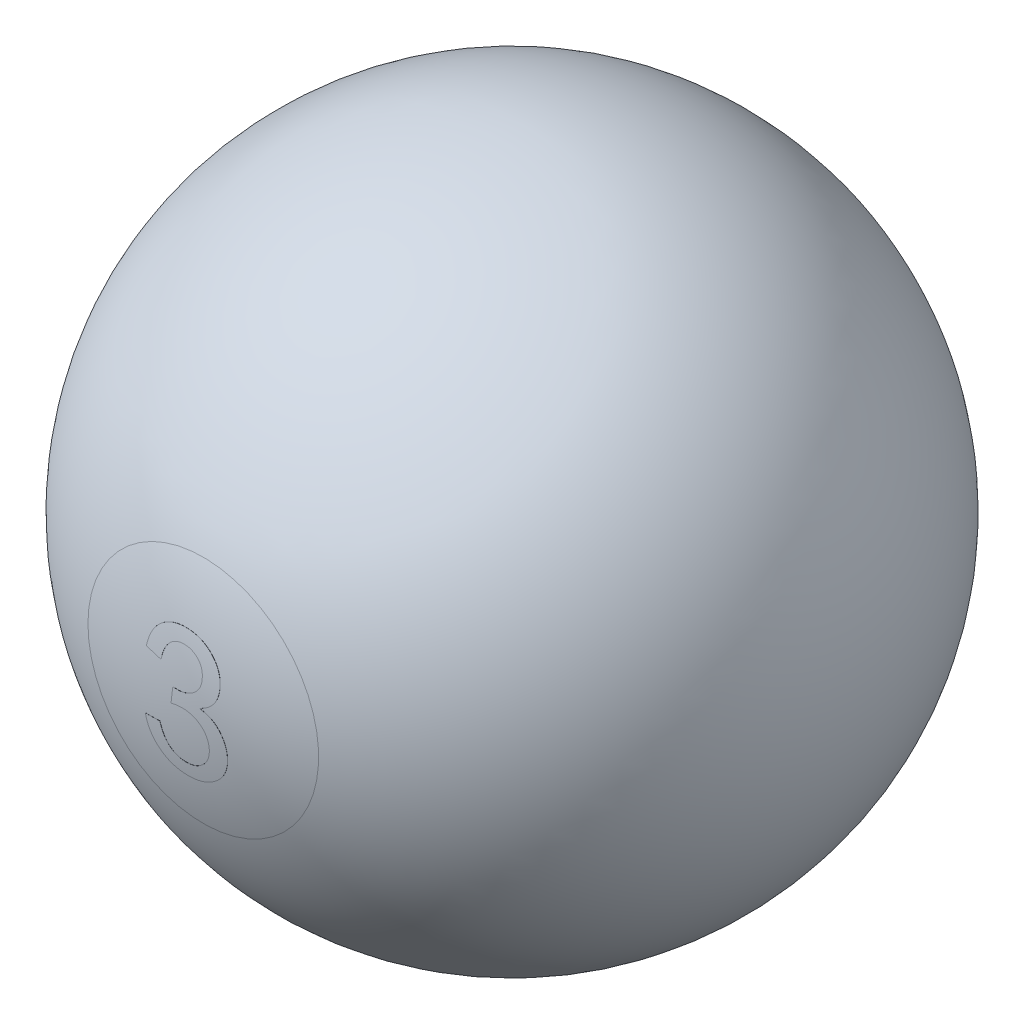
SolidWorks part; units mm, degrees
ref_plane "Vorne" through (0, 0, 0) normal (0, 0, 1) x (1, 0, 0)
ref_plane "Oben" through (0, 0, 0) normal (0, 1, 0) x (1, 0, 0)
ref_plane "Rechts" through (0, 0, 0) normal (1, 0, 0) x (0, 0, -1)
sketch "Skizze1" plane through (0, 0, 0) normal (0, 0, 1) x (1, 0, 0)
  line L0 (0, 0) -> (34.9607, 0) construction
  line L1 (28.575, 0) -> (-28.575, 0)
  arc A0 (28.575, 0) -> (-28.575, 0) centre (0, 0) ccw
  dimension "D1" = 57.15
revolve "Rotation1" add sketch "Skizze1" angle 360 about L0
sketch "Skizze2" plane through (0, 0, 0) normal (0, 0, 1) x (1, 0, 0)
  circle A0 centre (0, 0) radius 10
  dimension "D1" = 20
split line "Trennlinie_Schrift"
sketch "Skizze3" plane through (0, 0, 0) normal (0, 0, 1) x (1, 0, 0)
  line L0 (0, 0) -> (38.1, 0) construction
  line L1 (-38.1, 19.05) -> (38.1, 19.05)
  line L2 (-38.1, 19.05) -> (-38.1, -19.05)
  line L3 (-38.1, -19.05) -> (38.1, -19.05)
  line L4 (38.1, 19.05) -> (38.1, -19.05)
  line L7 (0, 0) -> (0, -19.05) construction
  dimension "D1" = 38.1
split line "Trennlinie_Halb"
ref_axis "Achse1" through (0, 31.4325, 0) along (0, -1, 0)
sketch "Skizze4" plane through (0, 0, 0) normal (0, 0, 1) x (1, 0, 0)
  line L0 (0, 0) -> (0, -5.7) construction
  line L3 (-10, -5.7) -> (10, -5.7) construction
  text T0 "1" font "@Arial Unicode MS" height 11
  dimension "D3" = 5.7
  dimension "D4" = 20
extrude "Linear austragen1" add sketch "Skizze4" along normal offset from surface (28.0529 mm away) 0.01
pattern_circular "Kreismuster1" count 2 over 360 about axis through (0, 31.4325, 0) along (0, -1, 0)
sketch "Skizze5" plane through (0, 0, 0) normal (0, 0, 1) x (1, 0, 0)
  text T0 "2"
extrude "Linear austragen2" add sketch "Skizze5" along normal offset from surface (28.1712 mm away) 0.01
pattern_circular "Kreismuster2" count 2 over 360 about axis through (0, 31.4325, 0) along (0, -1, 0)
sketch "Skizze6" plane through (0, 0, 0) normal (0, 0, 1) x (1, 0, 0)
  text T0 "3"
extrude "Linear austragen3" add sketch "Skizze6" along normal offset from surface (28.3199 mm away) 0.01
pattern_circular "Kreismuster3" count 2 over 360 about axis through (0, 31.4325, 0) along (0, -1, 0) of "Linear austragen3"
sketch "Skizze7" plane through (0, 0, 0) normal (0, 0, 1) x (1, 0, 0)
  text T0 "4"
extrude "Linear austragen4" add sketch "Skizze7" along normal offset from surface (28.4449 mm away) 0.01
pattern_circular "Kreismuster5" count 2 over 360 about axis through (0, 31.4325, 0) along (0, -1, 0)
sketch "Skizze8" plane through (0, 0, 0) normal (0, 0, 1) x (1, 0, 0)
  text T0 "5"
extrude "Linear austragen5" add sketch "Skizze8" along normal offset from surface (28.1304 mm away) 0.01
pattern_circular "Kreismuster6" count 2 over 360 about axis through (0, 31.4325, 0) along (0, -1, 0)
sketch "Skizze9" plane through (0, 0, 0) normal (0, 0, 1) x (1, 0, 0)
  text T0 "6" font "@Arial Unicode MS" height 11
extrude "Linear austragen6" add sketch "Skizze9" along normal offset from surface (28.2802 mm away) 0.01
sketch "Skizze10" plane through (0, 0, 0) normal (0, 0, 1) x (1, 0, 0)
  line L0 (0.15, -2.3) -> (0.15, -7.0671) construction
  line L1 (-3.0265, -5.4875) -> (0.15, -2.3) construction
  line L2 (0.15, -2.3) -> (3.3265, -5.4875) construction
  arc A0 (-2.6735, -5.1333) -> (2.9735, -5.1333) centre (0.15, -2.3) ccw
  arc A1 (-3.0265, -5.4875) -> (3.3265, -5.4875) centre (0.15, -2.3) ccw
  arc A2 (2.9735, -5.1333) -> (3.3265, -5.4875) centre (3.15, -5.3104) cw
  arc A3 (-2.6735, -5.1333) -> (-3.0265, -5.4875) centre (-2.85, -5.3104) ccw
  dimension "D1" = 4
  dimension "D2" = 4.5
  dimension "D3" = 6
  dimension "D4" = 2.3
  dimension "D5" = 0.15
extrude "Linear austragen7" add sketch "Skizze10" along normal offset from surface (27.9626 mm away) 0.01
pattern_circular "Kreismuster8" count 2 over 360 about axis through (0, 31.4325, 0) along (0, -1, 0)
sketch "Skizze11" plane through (0, 0, 0) normal (0, 0, 1) x (1, 0, 0)
  text T0 "7"
extrude "Linear austragen8" add sketch "Skizze11" along normal offset from surface (27.8882 mm away) 0.01
pattern_circular "Kreismuster9" count 2 over 360 about axis through (0, 31.4325, 0) along (0, -1, 0)
sketch "Skizze12" plane through (0, 0, 0) normal (0, 0, 1) x (1, 0, 0)
  text T0 "8"
extrude "Linear austragen9" add sketch "Skizze12" along normal offset from surface (28.309 mm away) 0.01
pattern_circular "Kreismuster11" count 2 over 360 about axis through (0, 31.4325, 0) along (0, -1, 0)
sketch "Skizze13" plane through (0, 0, 0) normal (0, 0, 1) x (1, 0, 0)
  text T0 "9"
extrude "Linear austragen10" add sketch "Skizze13" along normal offset from surface (28.1947 mm away) 0.01
sketch "Skizze14" plane through (0, 0, 0) normal (0, 0, 1) x (1, 0, 0)
  line L0 (-0.35, -2.3) -> (-0.35, -7.0671) construction
  line L1 (-3.5265, -5.4875) -> (-0.35, -2.3) construction
  line L2 (-0.35, -2.3) -> (2.8265, -5.4875) construction
  arc A0 (-3.1735, -5.1333) -> (2.4735, -5.1333) centre (-0.35, -2.3) ccw
  arc A1 (-3.5265, -5.4875) -> (2.8265, -5.4875) centre (-0.35, -2.3) ccw
  arc A2 (2.4735, -5.1333) -> (2.8265, -5.4875) centre (2.65, -5.3104) cw
  arc A3 (-3.1735, -5.1333) -> (-3.5265, -5.4875) centre (-3.35, -5.3104) ccw
  dimension "D1" = 4
  dimension "D2" = 4.5
  dimension "D3" = 6
  dimension "D4" = 0.35
  dimension "D5" = 2.3
extrude "Linear austragen11" add sketch "Skizze14" along normal offset from surface (28.0113 mm away) 0.01
pattern_circular "Kreismuster12" count 2 over 360 about axis through (0, 31.4325, 0) along (0, -1, 0)
sketch "Skizze15" plane through (0, 0, 0) normal (0, 0, 1) x (1, 0, 0)
  text T0 "10"
extrude "Linear austragen12" add sketch "Skizze15" along normal offset from surface (27.8338 mm away) 0.01
pattern_circular "Kreismuster13" count 2 over 360 about axis through (0, 31.4325, 0) along (0, -1, 0)
sketch "Skizze16" plane through (0, 0, 0) normal (0, 0, 1) x (1, 0, 0)
  text T0 "11"
extrude "Linear austragen13" add sketch "Skizze16" along normal offset from surface (27.8338 mm away) 0.01
pattern_circular "Kreismuster14" count 2 over 360 about axis through (0, 31.4325, 0) along (0, -1, 0)
sketch "Skizze17" plane through (0, 0, 0) normal (0, 0, 1) x (1, 0, 0)
  text T0 "12"
extrude "Linear austragen14" add sketch "Skizze17" along normal offset from surface (27.8338 mm away) 0.01
pattern_circular "Kreismuster15" count 2 over 360 about axis through (0, 31.4325, 0) along (0, -1, 0)
sketch "Skizze18" plane through (0, 0, 0) normal (0, 0, 1) x (1, 0, 0)
  text T0 "13"
extrude "Linear austragen15" add sketch "Skizze18" along normal offset from surface (27.8338 mm away) 0.01
pattern_circular "Kreismuster16" count 2 over 360 about axis through (0, 31.4325, 0) along (0, -1, 0)
sketch "Skizze19" plane through (0, 0, 0) normal (0, 0, 1) x (1, 0, 0)
  text T0 "14"
extrude "Linear austragen16" add sketch "Skizze19" along normal offset from surface (27.8338 mm away) 0.01
pattern_circular "Kreismuster17" count 2 over 360 about axis through (0, 31.4325, 0) along (0, -1, 0)
sketch "Skizze20" plane through (0, 0, 0) normal (0, 0, 1) x (1, 0, 0)
  text T0 "15"
extrude "Linear austragen17" add sketch "Skizze20" along normal offset from surface (27.8338 mm away) 0.01
pattern_circular "Kreismuster18" count 2 over 360 about axis through (0, 31.4325, 0) along (0, -1, 0)
